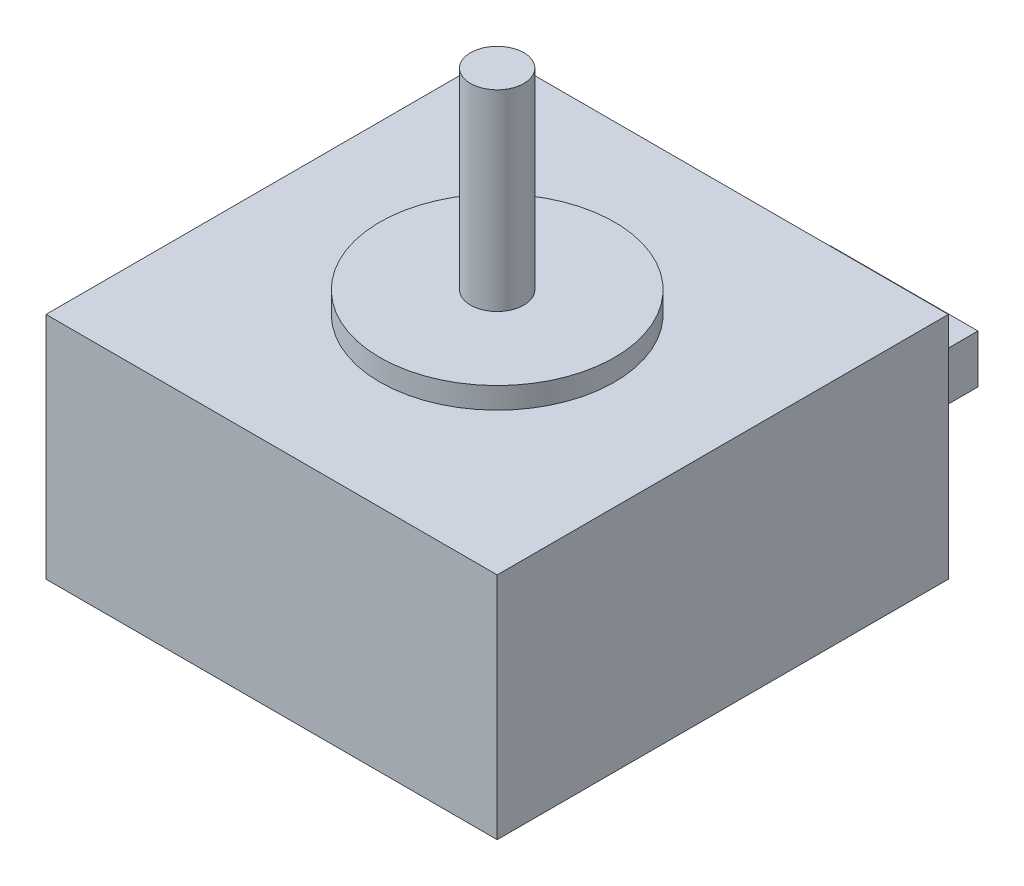
SolidWorks part; units mm, degrees
ref_plane "Front Plane" through (0, 0, 0) normal (0, 0, 1) x (1, 0, 0)
ref_plane "Top Plane" through (0, 0, 0) normal (0, 1, 0) x (1, 0, 0)
ref_plane "Right Plane" through (0, 0, 0) normal (1, 0, 0) x (0, 0, -1)
sketch "Sketch1" plane through (0, 0, 0) normal (0, 1, 0) x (1, 0, 0)
  line L1 (-36.3444, 15.3471) -> (5.9556, 15.3471)
  line L2 (-36.3444, 15.3471) -> (-36.3444, -26.9529)
  line L3 (-36.3444, -26.9529) -> (5.9556, -26.9529)
  line L4 (5.9556, 15.3471) -> (5.9556, -26.9529)
  dimension "D1" = 42.3
extrude "Boss-Extrude1" add sketch "Sketch1" along normal blind 21.5
sketch "Sketch2" plane through (0, 21.5, 0) normal (0, 1, 0) x (1, 0, 0)
  line L0 (-36.3444, 15.3471) -> (5.9556, -26.9529) construction
  line L1 (-36.3444, -26.9529) -> (5.9556, -26.9529) construction
  line L2 (5.9556, -26.9529) -> (5.9556, 15.3471) construction
  circle A0 centre (-15.1944, -5.8029) radius 11
  dimension "D1" = 22
extrude "Boss-Extrude2" add sketch "Sketch2" along normal blind 2
sketch "Sketch3" plane through (0, 23.5, 0) normal (0, 1, 0) x (1, 0, 0)
  circle A0 centre (-15.1944, -5.8029) radius 2.5
  dimension "D1" = 5
extrude "Boss-Extrude3" add sketch "Sketch3" along normal blind 18
sketch "Sketch4" plane through (0, 0, -15.3471) normal (0, 0, -1) x (-1, 0, 0)
  line L0 (-5.9556, 0) -> (36.3444, 0) construction
  line L1 (8.2681, 4.5425) -> (22.1207, 4.5425)
  line L2 (8.2681, 4.5425) -> (8.2681, 0)
  line L3 (8.2681, 0) -> (22.1207, 0)
  line L4 (22.1207, 4.5425) -> (22.1207, 0)
  line L5 (15.1944, 21.5) -> (15.1944, 17.176) construction
  line L6 (-5.9556, 21.5) -> (36.3444, 21.5) construction
extrude "Boss-Extrude4" add sketch "Sketch4" along normal blind 17
